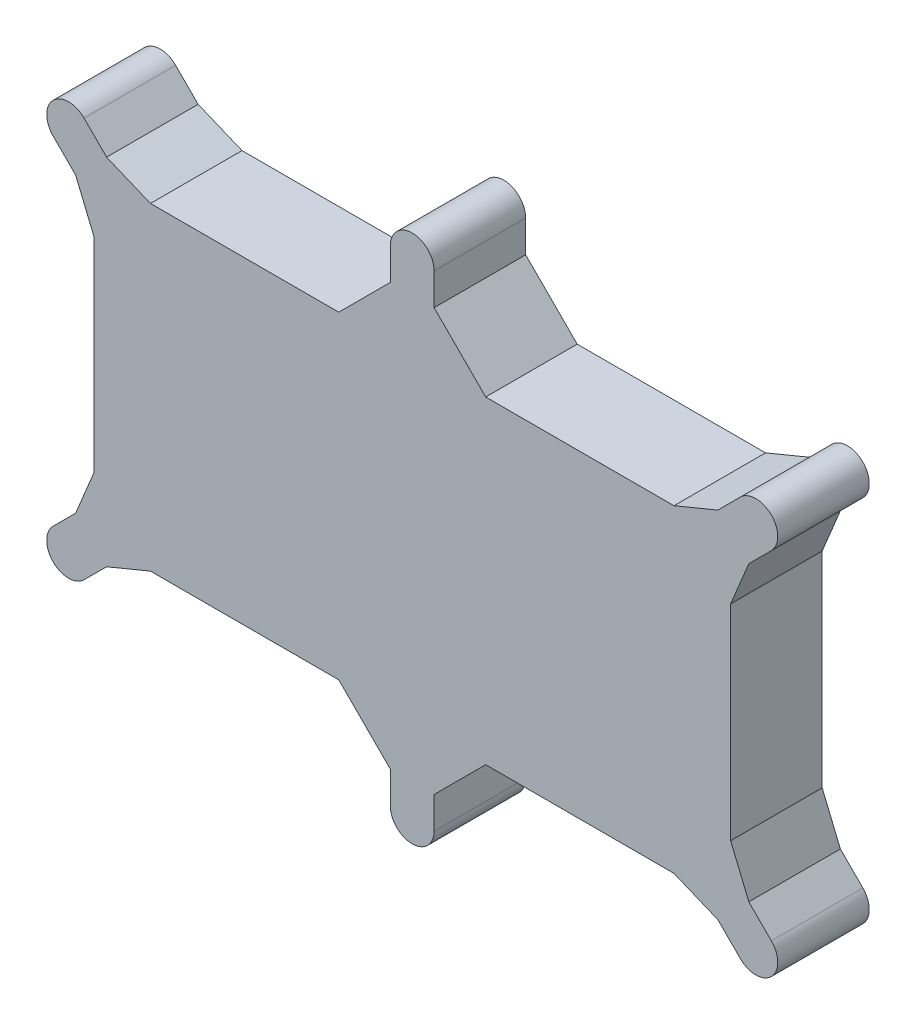
SolidWorks part; units mm, degrees
ref_plane "Спереди" through (0, 0, 0) normal (0, 0, 1) x (1, 0, 0)
ref_plane "Сверху" through (0, 0, 0) normal (0, 1, 0) x (1, 0, 0)
ref_plane "Справа" through (0, 0, 0) normal (1, 0, 0) x (0, 0, -1)
sketch "Эскиз3" plane through (0, 0, 0) normal (0, 0, 1) x (1, 0, 0)
  line L0 (0, 0) -> (160, 0) construction
  line L1 (0, 0) -> (0, 80) construction
  line L2 (0, 80) -> (0, 121.91) construction
  line L3 (0, 80) -> (160, 80) construction
  line L4 (160, 80) -> (160, 0) construction
  line L5 (160, 80) -> (166.0213, 86.0213) construction
  line L6 (0, 94.41) -> (7, 94.41) construction
  line L8 (7, 94.41) -> (7, 101.41) construction
  line L9 (7, 101.41) -> (7.75, 101.41) construction
  line L10 (7.75, 101.41) -> (7.75, 114.63) construction
  line L28 (11, 121.91) -> (11, 105.91)
  line L31 (11, 105.91) -> (36.91, 80)
  line L32 (0, 121.91) -> (0, 132.91) construction
  line L39 (180.4425, 84.8861) -> (169.1287, 73.5724)
  line L41 (169.1287, 73.5724) -> (160, 51.5337)
  line L43 (164.8861, 100.4425) -> (153.5724, 89.1287)
  line L44 (153.5724, 89.1287) -> (131.5337, 80)
  line L45 (36.91, 80) -> (131.5337, 80)
  line L47 (160, 51.5337) -> (160, -51.5337)
  line L48 (-160, 51.5337) -> (-160, -51.5337)
  line L49 (-169.1287, 73.5724) -> (-160, 51.5337)
  line L50 (-180.4425, 84.8861) -> (-169.1287, 73.5724)
  line L51 (-164.8861, 100.4425) -> (-153.5724, 89.1287)
  line L52 (-153.5724, 89.1287) -> (-131.5337, 80)
  line L53 (-36.91, 80) -> (-131.5337, 80)
  line L54 (-11, 105.91) -> (-36.91, 80)
  line L55 (-11, 121.91) -> (-11, 105.91)
  line L56 (169.1287, -73.5724) -> (160, -51.5337)
  line L57 (180.4425, -84.8861) -> (169.1287, -73.5724)
  line L58 (164.8861, -100.4425) -> (153.5724, -89.1287)
  line L59 (153.5724, -89.1287) -> (131.5337, -80)
  line L60 (36.91, -80) -> (131.5337, -80)
  line L61 (11, -105.91) -> (36.91, -80)
  line L62 (11, -121.91) -> (11, -105.91)
  line L63 (-11, -121.91) -> (-11, -105.91)
  line L64 (-11, -105.91) -> (-36.91, -80)
  line L65 (-36.91, -80) -> (-131.5337, -80)
  line L66 (-153.5724, -89.1287) -> (-131.5337, -80)
  line L67 (-164.8861, -100.4425) -> (-153.5724, -89.1287)
  line L68 (-180.4425, -84.8861) -> (-169.1287, -73.5724)
  line L69 (-169.1287, -73.5724) -> (-160, -51.5337)
  line L76 (-172.6643, 92.6643) -> (0, 121.91) construction
  line L77 (0, 121.91) -> (172.6643, 92.6643) construction
  line L78 (172.6643, 92.6643) -> (172.6643, -92.6643) construction
  line L79 (172.6643, -92.6643) -> (0, -121.91) construction
  line L80 (0, -121.91) -> (-172.6643, -92.6643) construction
  line L81 (-172.6643, -92.6643) -> (-172.6643, 92.6643) construction
  line L82 (0, 121.91) -> (0, -121.91) construction
  line L83 (0, 132.91) -> (0, -132.91) construction
  line L84 (180.4425, 80) -> (0, 80) construction
  line L85 (180.4425, 80) -> (180.4425, 100.4425) construction
  line L86 (180.4425, 80) -> (180.4425, 0) construction
  line L87 (180.4425, 0) -> (160, 0) construction
  circle A124 centre (0, 121.91) radius 11 construction
  arc A129 (11, 121.91) -> (-11, 121.91) centre (0, 121.91) ccw
  circle A134 centre (172.6643, 92.6643) radius 11 construction
  arc A135 (180.4425, 84.8861) -> (164.8861, 100.4425) centre (172.6643, 92.6643) ccw
  arc A142 (-180.4425, 84.8861) -> (-164.8861, 100.4425) centre (-172.6643, 92.6643) cw
  arc A148 (180.4425, -84.8861) -> (164.8861, -100.4425) centre (172.6643, -92.6643) cw
  arc A159 (11, -121.91) -> (-11, -121.91) centre (0, -121.91) cw
  arc A167 (-180.4425, -84.8861) -> (-164.8861, -100.4425) centre (-172.6643, -92.6643) ccw
  point P7 (151.5147, 71.5147)
  point P9 (0, 94.41)
  point P17 (11, 121.91)
  point P24 (0, 132.91)
  point P26 (172.6643, 92.6643)
  point P39 (180.4425, 100.4425)
  point P134 (-160, 0)
  point P160 (0, 92)
  dimension "D10" = 7.75
  dimension "D11" = 7
  dimension "D13" = 135
  dimension "D20" = 12
  dimension "D14" = 29.91
  dimension "D12" = 13.22
  dimension "D5" = 22
  dimension "D1" = 135
  dimension "D2" = 80
  dimension "D3" = 160
  dimension "D4" = 29.91
  dimension "D8" = 12
  dimension "D9" = 7
  dimension "D21" = 22.5
  dimension "D27" = 16
  dimension "D28" = 2.41
  dimension "D29" = 16
extrude "Бобышка-Вытянуть3" add sketch "Эскиз3" along normal blind 46
